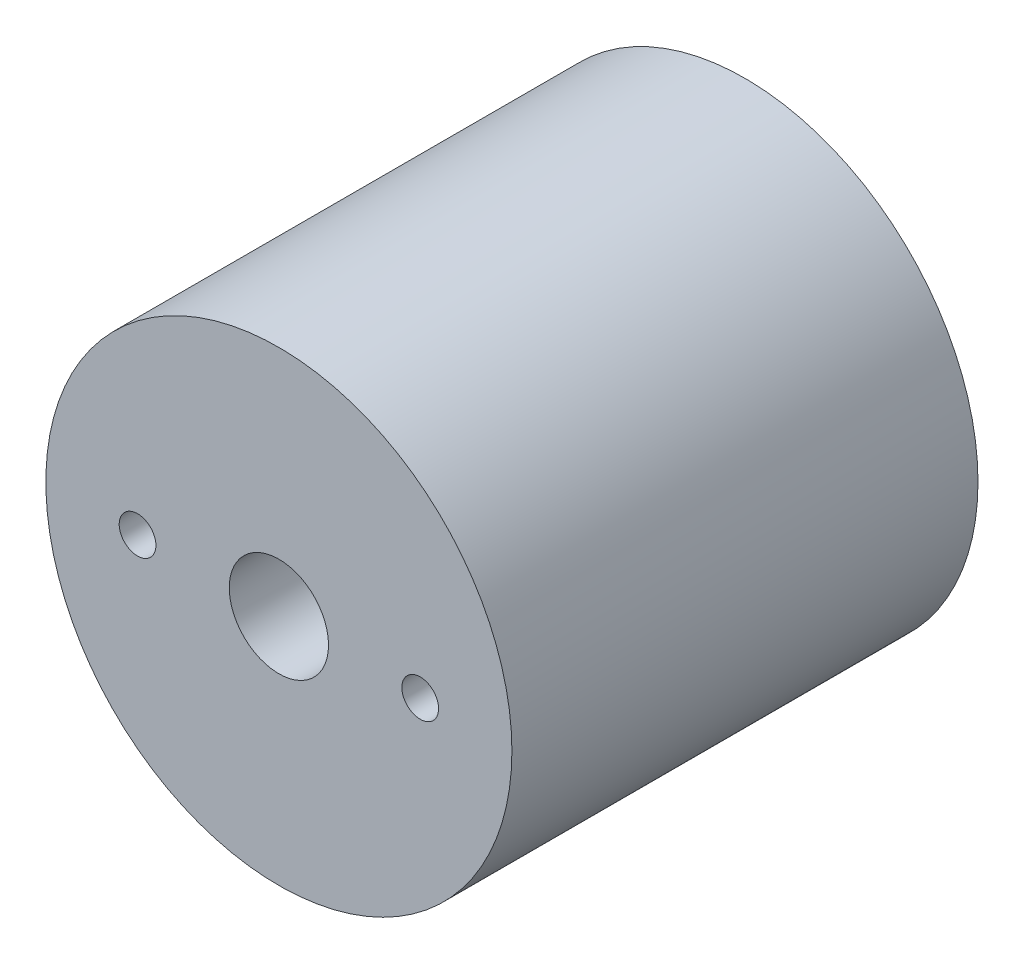
SolidWorks part; units mm, degrees
ref_plane "Front Plane" through (0, 0, 0) normal (0, 0, 1) x (1, 0, 0)
ref_plane "Top Plane" through (0, 0, 0) normal (0, 1, 0) x (1, 0, 0)
ref_plane "Right Plane" through (0, 0, 0) normal (1, 0, 0) x (0, 0, -1)
sketch "Sketch1" plane through (0, 0, 0) normal (0, 0, 1) x (1, 0, 0)
  circle A0 centre (0, 0) radius 12.7
extrude "Boss-Extrude1" add sketch "Sketch1" along normal blind 25.4
sketch "Sketch2" plane through (0, 0, 0) normal (0, 0, -1) x (-1, 0, 0)
  circle A0 centre (0, 0) radius 10.4
extrude "Cut-Extrude1" cut sketch "Sketch2" against normal blind 5.5
sketch "Sketch3" plane through (0, 0, 0) normal (0, 0, -1) x (-1, 0, 0)
  circle A0 centre (0, 0) radius 11.75
  dimension "D1" = 23.5
extrude "Cut-Extrude2" cut sketch "Sketch3" against normal blind 1.8 from offset 1 offset against normal yes
hole_wizard "1/4-28 Tapped Hole1" positions "Sketch7" profile "Sketch6" tap size "1/4-28" standard "Ansi Inch" end condition through all
sketch "Sketch7" plane through (0, 0, 25.4) normal (0, 0, 1) x (1, 0, 0)
  point P0 (0, 0)
sketch "Sketch6" plane through (0, 0, 25.4) normal (1, 0, 0) x (0, -1, 0)
  line L0 (0, 0) -> (0, 25.4)
  line L1 (0, 25.4) -> (2.7051, 25.4)
  line L2 (2.7051, 25.4) -> (2.7051, 0)
  line L5 (2.7051, 0) -> (0, 0)
  line L11 (0, -6.35) -> (0, 107.95) construction
  dimension "Thru Tap Drill Dia." = 5.4102
  dimension "Thru Tap Drill Depth" = 25.4
cosmetic thread "Hole Thread1" parameters "D2"=6.35
ref_axis "Axis1" through (0, 0, 29.736) along (0, 0, -1)
sketch "Sketch10" plane through (0, 0, 0) normal (0, 1, 0) x (1, 0, 0)
  line L0 (0, -25.4023) -> (8.6546, -5.5)
  line L1 (8.6546, -5.5) -> (0, -5.5)
  line L2 (0, -5.5) -> (0, -25.4023)
  line L3 (2.7051, -5.5) -> (-2.7051, -5.5) construction
  line L4 (0, -29.736) -> (0, 17.4859) construction
revolve "Cut-Revolve1" cut sketch "Sketch10" angle 360 about axis through (0, 0, 29.736) along (0, 0, -1)
sketch "Sketch11" plane through (0, 0, 25.4) normal (0, 0, 1) x (1, 0, 0)
  line L0 (-2.7051, 0) -> (-12.7, 0) construction
  line L1 (0, 0) -> (0, 10.3093) construction
  circle A0 centre (0, 0) radius 2.7051 construction
  circle A1 centre (0, 0) radius 12.7 construction
  circle A2 centre (-7.7025, 0) radius 1
  circle A3 centre (7.7025, 0) radius 1
  dimension "D1" = 2
extrude "Cut-Extrude3" cut sketch "Sketch11" against normal through all
